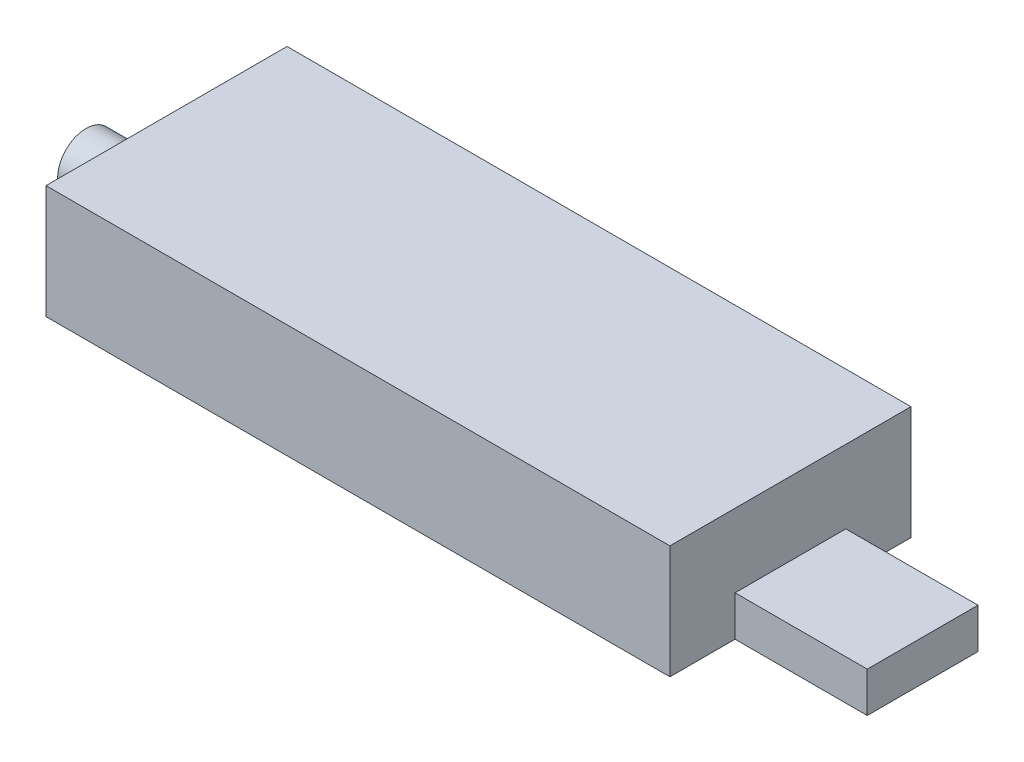
SolidWorks part; units mm, degrees
material "ABS"
ref_plane "Front Plane" through (0, 0, 0) normal (0, 0, 1) x (1, 0, 0)
ref_plane "Top Plane" through (0, 0, 0) normal (0, 1, 0) x (1, 0, 0)
ref_plane "Right Plane" through (0, 0, 0) normal (1, 0, 0) x (0, 0, -1)
sketch "Sketch1" plane through (0, 0, 0) normal (0, 1, 0) x (1, 0, 0)
  line L1 (0, 0) -> (69.85, 0)
  line L2 (0, 0) -> (0, 26.9875)
  line L3 (0, 26.9875) -> (69.85, 26.9875)
  line L4 (69.85, 0) -> (69.85, 26.9875)
  dimension "D1" = 69.85
  dimension "D2" = 26.9875
extrude "Boss-Extrude1" add sketch "Sketch1" along normal blind 12.7
sketch "Sketch2" plane through (69.85, 0, 0) normal (1, 0, 0) x (0, 0, -1)
  line L0 (0, 0) -> (26.9875, 0) construction
  line L1 (7.2937, 0) -> (19.6937, 0)
  line L2 (7.2937, 0) -> (7.2937, 4.5)
  line L3 (7.2937, 4.5) -> (19.6937, 4.5)
  line L4 (19.6937, 0) -> (19.6937, 4.5)
  point P6 (13.4937, 0)
  dimension "D1" = 12.4
  dimension "D2" = 4.5
extrude "Boss-Extrude2" add sketch "Sketch2" along normal blind 14.8
ref_plane "Plane1" through (-9.0125, 0, 0) normal (1, 0, 0) x (0, 0, -1)
sketch "Sketch3" plane through (0, 0, 0) normal (-1, 0, 0) x (0, 0, 1)
  line L0 (-26.9875, 0) -> (0, 0) construction
  line L1 (-13.4937, 3.81) -> (-13.4937, 0) construction
  circle A0 centre (-13.4937, 3.81) radius 3.175
  dimension "D1" = 6.35
  dimension "D2" = 3.81
extrude "Boss-Extrude3" add sketch "Sketch3" along normal up to surface (9.0125 mm away) up to plane "Plane1"
